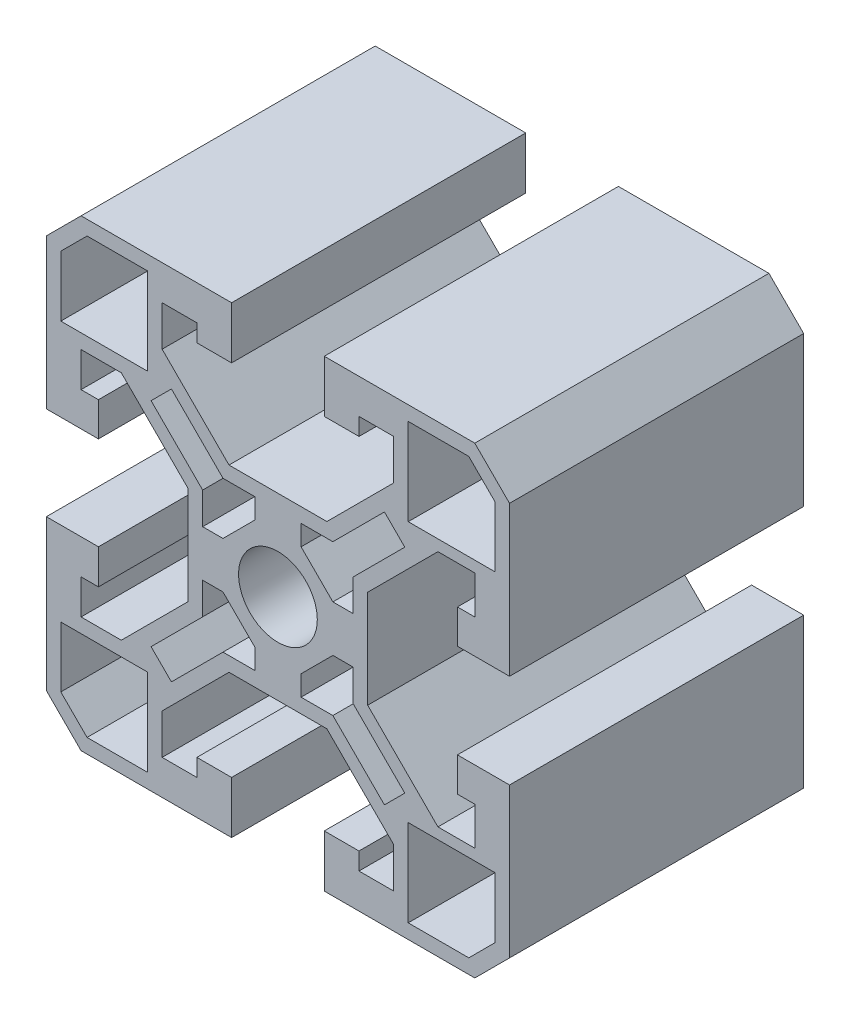
SolidWorks part; units mm, degrees
material "6061 Alloy"
ref_plane "Front" through (0, 0, 0) normal (0, 0, 1) x (1, 0, 0)
ref_plane "Top" through (0, 0, 0) normal (0, 1, 0) x (1, 0, 0)
ref_plane "Right" through (0, 0, 0) normal (1, 0, 0) x (0, 0, -1)
sketch "Sketch1" plane through (0, 0, 0) normal (0, 0, 1) x (1, 0, 0)
  line L0 (4.225, 7.75) -> (-4.225, 7.75)
  line L1 (-4.225, 7.75) -> (-10, 13.525)
  line L2 (10, 13.525) -> (4.225, 7.75)
  line L3 (-10, 13.525) -> (-10, 17)
  line L4 (10, 17) -> (10, 13.525)
  line L5 (-10, 17) -> (-7, 17)
  line L6 (7, 17) -> (10, 17)
  line L7 (-7, 17) -> (-7, 15.5)
  line L8 (7, 15.5) -> (7, 17)
  line L9 (-7, 15.5) -> (-4, 15.5)
  line L10 (4, 15.5) -> (7, 15.5)
  line L11 (-4, 15.5) -> (-4, 20)
  line L12 (4, 20) -> (4, 15.5)
  line L13 (-4, 20) -> (-17, 20)
  line L14 (17, 20) -> (4, 20)
  line L15 (-17, 20) -> (-20, 17)
  line L16 (20, 17) -> (17, 20)
  line L17 (-20, 17) -> (-20, 4.0635)
  line L18 (20, 4.0635) -> (20, 17)
  line L19 (-20, 4.0635) -> (-15.5, 4.0635)
  line L20 (15.5, 4.0635) -> (20, 4.0635)
  line L21 (-15.5, 4.0635) -> (-15.5, 7)
  line L22 (15.5, 7) -> (15.5, 4.0635)
  line L23 (-15.5, 7) -> (-17, 7)
  line L24 (17, 7) -> (15.5, 7)
  line L25 (-17, 7) -> (-17, 10)
  line L26 (17, 10.2921) -> (17, 7)
  line L27 (-17, 10) -> (-13.525, 10)
  line L28 (13.8171, 10.2921) -> (17, 10.2921)
  line L29 (-13.525, 10) -> (-7.75, 4.225)
  line L30 (7.75, 4.225) -> (13.8171, 10.2921)
  line L31 (-7.75, 4.225) -> (-7.75, -4.225)
  line L32 (7.75, -4.225) -> (7.75, 4.225)
  line L33 (-7.75, -4.225) -> (-13.525, -10)
  line L34 (13.8171, -10.2921) -> (7.75, -4.225)
  line L35 (-13.525, -10) -> (-17, -10)
  line L36 (17, -10.2921) -> (13.8171, -10.2921)
  line L37 (-17, -10) -> (-17, -7)
  line L38 (17, -7) -> (17, -10.2921)
  line L39 (-17, -7) -> (-15.5, -7)
  line L40 (15.5, -7) -> (17, -7)
  line L41 (-15.5, -7) -> (-15.5, -4)
  line L42 (15.5, -4.0635) -> (15.5, -7)
  line L43 (-15.5, -4) -> (-20, -4)
  line L44 (20, -4.0635) -> (15.5, -4.0635)
  line L45 (-20, -4) -> (-20, -17)
  line L46 (20, -17) -> (20, -4.0635)
  line L47 (-20, -17) -> (-17, -20)
  line L48 (17, -20) -> (20, -17)
  line L49 (-17, -20) -> (-4, -20)
  line L50 (4, -20) -> (17, -20)
  line L51 (-4, -20) -> (-4, -15.5)
  line L52 (4, -15.5) -> (4, -20)
  line L53 (-4, -15.5) -> (-7, -15.5)
  line L54 (7, -15.5) -> (4, -15.5)
  line L55 (-7, -15.5) -> (-7, -17)
  line L56 (7, -17) -> (7, -15.5)
  line L57 (-7, -17) -> (-10, -17)
  line L58 (10, -17) -> (7, -17)
  line L59 (-10, -17) -> (-10, -13.525)
  line L60 (10, -13.525) -> (10, -17)
  line L61 (-10, -13.525) -> (-4.225, -7.75)
  line L62 (4.225, -7.75) -> (10, -13.525)
  line L63 (-4.225, -7.75) -> (4.225, -7.75)
  line L64 (-18.75, -16.4822) -> (-16.4822, -18.75)
  line L65 (-16.4822, -18.75) -> (-11.25, -18.75)
  line L66 (-18.75, -11.25) -> (-18.75, -16.4822)
  line L67 (-11.25, -18.75) -> (-11.25, -11.25)
  line L68 (-11.25, -11.25) -> (-18.75, -11.25)
  line L69 (18.75, 16.4822) -> (16.4822, 18.75)
  line L70 (16.4822, 18.75) -> (11.25, 18.75)
  line L71 (18.75, 11.25) -> (18.75, 16.4822)
  line L72 (11.25, 18.75) -> (11.25, 11.25)
  line L73 (11.25, 11.25) -> (18.75, 11.25)
  line L74 (2, -6.5) -> (4.7428, -6.5)
  line L75 (4.7428, -6.5) -> (9.1977, -10.9549)
  line L76 (2, -4.7458) -> (2, -6.5)
  line L77 (9.1977, -10.9549) -> (10.9549, -9.1977)
  line L78 (4.7458, -2) -> (2, -4.7458)
  line L79 (10.9549, -9.1977) -> (6.5, -4.7428)
  line L80 (6.5, -2) -> (4.7458, -2)
  line L81 (6.5, -4.7428) -> (6.5, -2)
  line L82 (6.5, 2) -> (6.5, 4.7428)
  line L83 (6.5, 4.7428) -> (10.9549, 9.1977)
  line L84 (4.7458, 2) -> (6.5, 2)
  line L85 (10.9549, 9.1977) -> (9.1977, 10.9549)
  line L86 (2, 4.7458) -> (4.7458, 2)
  line L87 (9.1977, 10.9549) -> (4.7428, 6.5)
  line L88 (2, 6.5) -> (2, 4.7458)
  line L89 (4.7428, 6.5) -> (2, 6.5)
  line L90 (-2, 6.5) -> (-4.7428, 6.5)
  line L91 (-4.7428, 6.5) -> (-9.1977, 10.9549)
  line L92 (-2, 4.7458) -> (-2, 6.5)
  line L93 (-9.1977, 10.9549) -> (-10.9549, 9.1977)
  line L94 (-4.7458, 2) -> (-2, 4.7458)
  line L95 (-10.9549, 9.1977) -> (-6.5, 4.7428)
  line L96 (-6.5, 2) -> (-4.7458, 2)
  line L97 (-6.5, 4.7428) -> (-6.5, 2)
  line L98 (-6.5, -2) -> (-6.5, -4.7428)
  line L99 (-6.5, -4.7428) -> (-10.9549, -9.1977)
  line L100 (-4.7458, -2) -> (-6.5, -2)
  line L101 (-10.9549, -9.1977) -> (-9.1977, -10.9549)
  line L102 (-2, -4.7458) -> (-4.7458, -2)
  line L103 (-9.1977, -10.9549) -> (-4.7428, -6.5)
  line L104 (-2, -6.5) -> (-2, -4.7458)
  line L105 (-4.7428, -6.5) -> (-2, -6.5)
  line L106 (-16.4822, 18.75) -> (-18.75, 16.4822)
  line L107 (-18.75, 16.4822) -> (-18.75, 11.25)
  line L108 (-11.25, 18.75) -> (-16.4822, 18.75)
  line L109 (-18.75, 11.25) -> (-11.25, 11.25)
  line L110 (-11.25, 11.25) -> (-11.25, 18.75)
  line L111 (16.4822, -18.75) -> (18.75, -16.4822)
  line L112 (18.75, -16.4822) -> (18.75, -11.25)
  line L113 (11.25, -18.75) -> (16.4822, -18.75)
  line L114 (18.75, -11.25) -> (11.25, -11.25)
  line L115 (11.25, -11.25) -> (11.25, -18.75)
  circle A0 centre (0, 0) radius 3.4
extrude "Extrude1" add sketch "Sketch1" along normal blind 25.4
